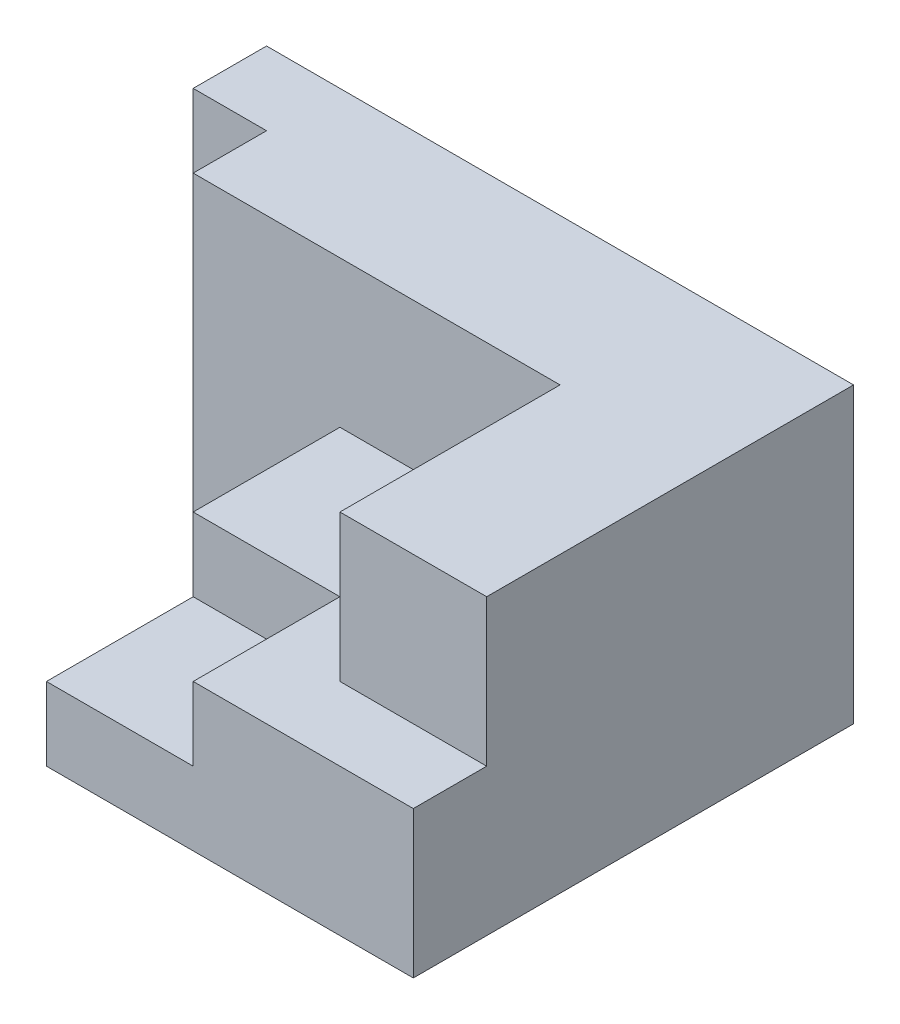
SolidWorks part; units mm, degrees
ref_plane "Front Plane" through (0, 0, 0) normal (0, 0, 1) x (1, 0, 0)
ref_plane "Top Plane" through (0, 0, 0) normal (0, 1, 0) x (1, 0, 0)
ref_plane "Right Plane" through (0, 0, 0) normal (1, 0, 0) x (0, 0, -1)
sketch "Sketch2" plane through (0, 0, 0) normal (0, 1, 0) x (1, 0, 0)
  line L0 (0, 0) -> (80, 0)
  line L1 (80, 0) -> (80, -60)
  line L2 (80, -60) -> (30, -60)
  line L3 (30, -60) -> (30, -20)
  line L4 (30, -20) -> (10, -20)
  line L5 (10, -20) -> (10, -10)
  line L6 (10, -10) -> (0, -10)
  line L7 (0, -10) -> (0, 0)
  dimension "D1" = 10
  dimension "D2" = 10
  dimension "D3" = 10
  dimension "D4" = 20
  dimension "D5" = 40
  dimension "D6" = 50
  dimension "D7" = 60
extrude "Boss-Extrude2" add sketch "Sketch2" along normal blind 40
sketch "Sketch3" plane through (0, 40, 0) normal (0, 1, 0) x (1, 0, 0)
  line L0 (80, -52.3527) -> (80, -60)
  line L1 (80, -60) -> (80, 0) construction
  line L2 (80, -60) -> (30, -60)
  line L3 (30, -20) -> (30, -60) construction
  line L4 (30, -60) -> (80, -60) construction
  line L5 (30, -60) -> (30, -20)
  line L6 (30, -20) -> (60, -20)
  line L7 (60, -20) -> (60, -50)
  line L8 (60, -50) -> (80, -50)
  line L9 (80, -50) -> (80, -52.3527)
  dimension "D1" = 20
  dimension "D2" = 30
  dimension "D3" = 2.3527
extrude "Cut-Extrude1" cut sketch "Sketch3" against normal blind 20
sketch "Sketch4" plane through (0, 20, 0) normal (0, 1, 0) x (1, 0, 0)
  line L1 (30, -60) -> (50, -60)
  line L2 (30, -60) -> (30, -40)
  line L3 (30, -40) -> (50, -40)
  line L4 (50, -60) -> (50, -40)
  dimension "D1" = 20
  dimension "D2" = 20
extrude "Cut-Extrude2" cut sketch "Sketch4" against normal blind 10
